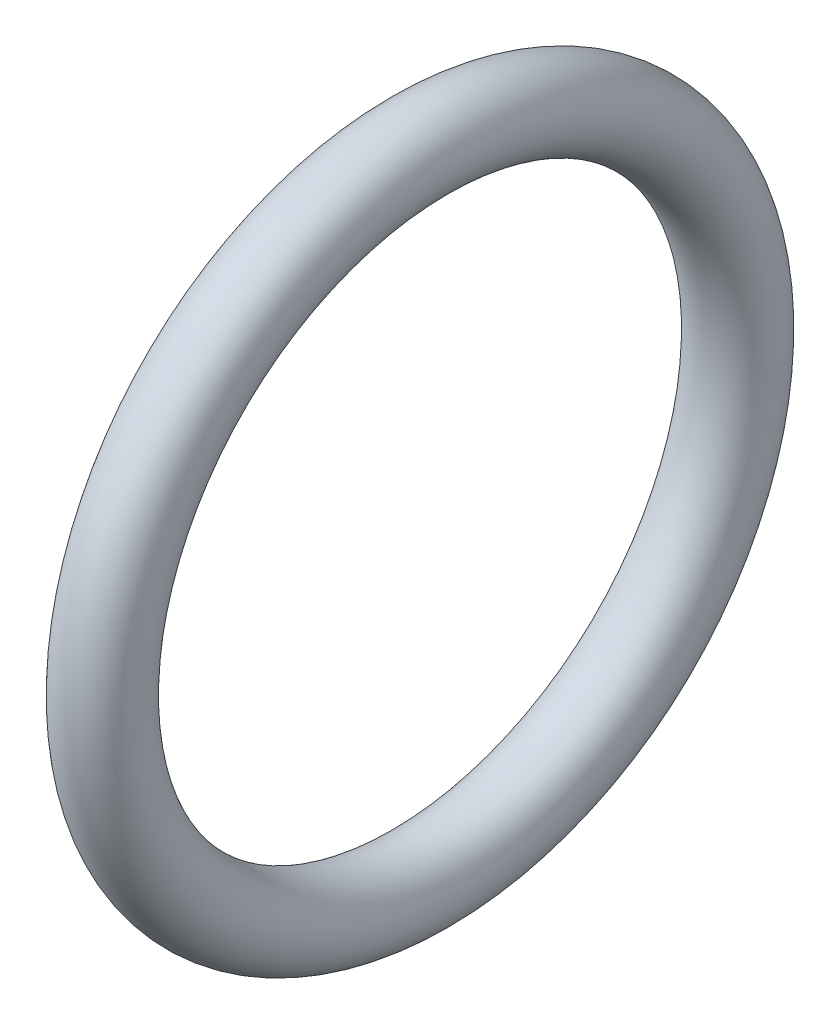
SolidWorks part; units mm, degrees
material "Silicon Rubber"
ref_plane "Front Plane" through (0, 0, 0) normal (0, 0, 1) x (1, 0, 0)
ref_plane "Top Plane" through (0, 0, 0) normal (0, 1, 0) x (1, 0, 0)
ref_plane "Right Plane" through (0, 0, 0) normal (1, 0, 0) x (0, 0, -1)
sketch "Sketch1" plane through (0, 0, 0) normal (0, 0, 1) x (1, 0, 0)
  line L0 (0, 0) -> (-5, 0) construction
  circle A0 centre (0, 4) radius 0.5
  dimension "D2" = 1
  dimension "D1" = 4
  dimension "D3" = 5
revolve "Revolve1" add sketch "Sketch1" angle 360 about L0
